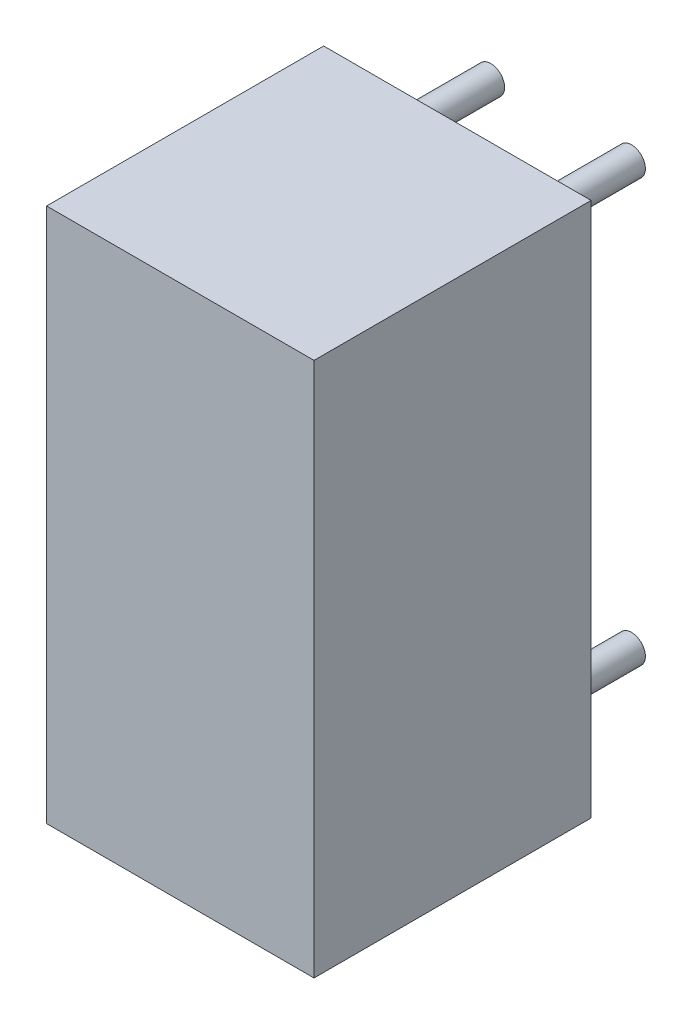
SolidWorks part; units mm, degrees
ref_plane "Front Plane" through (0, 0, 0) normal (0, 0, 1) x (1, 0, 0)
ref_plane "Top Plane" through (0, 0, 0) normal (0, 1, 0) x (1, 0, 0)
ref_plane "Right Plane" through (0, 0, 0) normal (1, 0, 0) x (0, 0, -1)
sketch "Sketch1" plane through (0, 0, 0) normal (0, 0, 1) x (1, 0, 0)
  line L0 (-1.016, 8.636) -> (-1.016, -1.016)
  line L1 (-1.016, -1.016) -> (3.81, -1.016)
  line L2 (3.81, -1.016) -> (3.81, 8.636)
  line L3 (3.81, 8.636) -> (-1.016, 8.636)
extrude "Component_Outline" add sketch "Sketch1" along normal blind 5 separate body
sketch "Sketch2" plane through (0, 0, 0) normal (0, 0, 1) x (1, 0, 0)
  circle A0 centre (0, 0) radius 0.25
extrude "1" add sketch "Sketch2" against normal blind 2 separate body
sketch "Sketch3" plane through (0, 0, 0) normal (0, 0, 1) x (1, 0, 0)
  circle A0 centre (2.54, 0) radius 0.25
extrude "2" add sketch "Sketch3" against normal blind 2 separate body
sketch "Sketch4" plane through (0, 0, 0) normal (0, 0, 1) x (1, 0, 0)
  circle A0 centre (2.54, 7.62) radius 0.25
extrude "3" add sketch "Sketch4" against normal blind 2 separate body
sketch "Sketch5" plane through (0, 0, 0) normal (0, 0, 1) x (1, 0, 0)
  circle A0 centre (0, 7.62) radius 0.25
extrude "4" add sketch "Sketch5" against normal blind 2 separate body
sketch3d "3DSketch1"
  line L0 (0, 0, 0) -> (1, 0, 0)
  line L1 (0, 0, 0) -> (0, 1, 0)
  line L2 (0, 0, 0) -> (0, 0, 1)
  point P0 (0, 0, 0)
